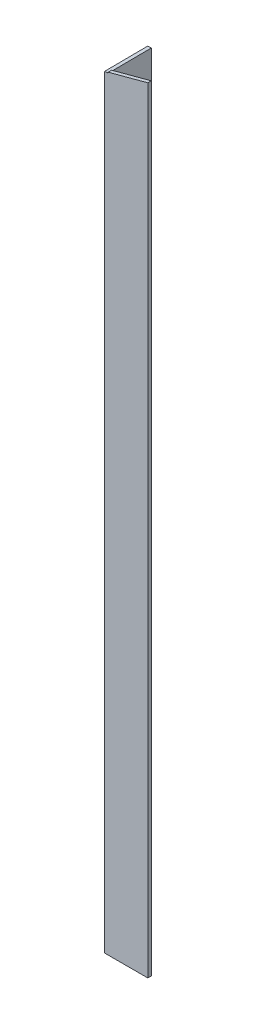
SolidWorks part; units mm, degrees
ref_plane "Спереди" through (0, 0, 0) normal (0, 0, 1) x (1, 0, 0)
ref_plane "Сверху" through (0, 0, 0) normal (0, 1, 0) x (1, 0, 0)
ref_plane "Справа" through (0, 0, 0) normal (1, 0, 0) x (0, 0, -1)
sketch "Эскиз1" plane through (0, 0, 0) normal (0, 1, 0) x (1, 0, 0)
  line L0 (0, 50) -> (0, 0)
  line L1 (0, 0) -> (50, 0)
extrude "Вытянуть-Тонкостенный1" add sketch "Эскиз1" along normal blind 900 thin thin type one direction reverse wall 4
sketch "Эскиз3" plane through (0, 0, 0) normal (0, 0, 1) x (1, 0, 0)
  line L0 (0, 900) -> (50, 900)
  line L1 (50, 900) -> (0, 886.6025)
  line L2 (0, 900) -> (0, 0) construction
  line L3 (0, 886.6025) -> (0, 900)
extrude "Вырез-Вытянуть1" cut sketch "Эскиз3" against normal blind 4
sketch "Эскиз4" plane through (0, 0, 0) normal (-1, 0, 0) x (0, 0, 1)
  line L0 (0, 900) -> (-50, 900)
  line L1 (-50, 900) -> (-4, 900) construction
  line L3 (0, 886.6025) -> (0, 900)
  line L4 (-50, 900) -> (-50, 887)
  line L5 (-50, 900) -> (-50, 0) construction
  line L6 (-50, 887) -> (0, 886.6025)
extrude "Вырез-Вытянуть2" cut sketch "Эскиз4" against normal blind 4
